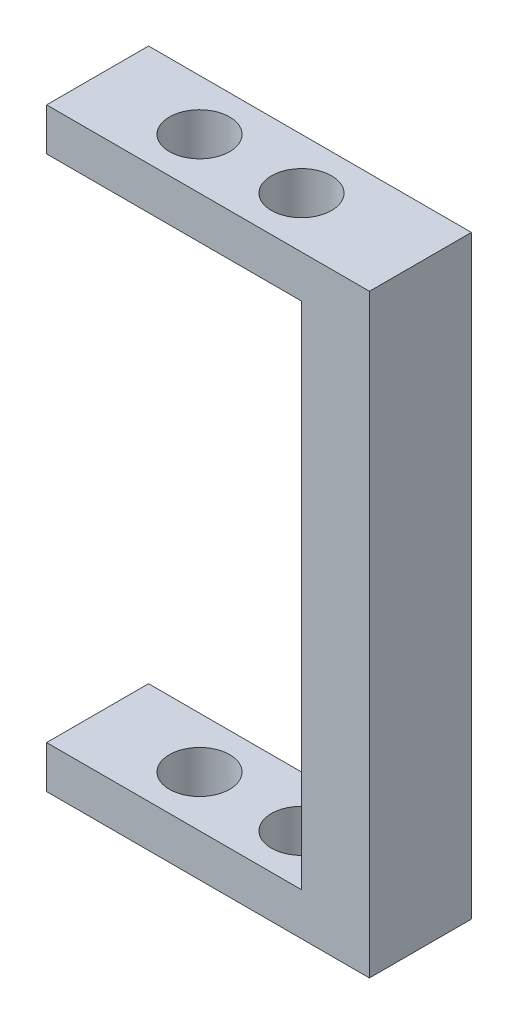
SolidWorks part; units mm, degrees
ref_plane "Front Plane" through (0, 0, 0) normal (0, 0, 1) x (1, 0, 0)
ref_plane "Top Plane" through (0, 0, 0) normal (0, 1, 0) x (1, 0, 0)
ref_plane "Right Plane" through (0, 0, 0) normal (1, 0, 0) x (0, 0, -1)
sketch "Sketch1" plane through (0, 0, 0) normal (0, 0, 1) x (1, 0, 0)
  line L1 (-2.54, -22.225) -> (2.54, -22.225)
  line L2 (-2.54, -22.225) -> (-2.54, 22.225)
  line L3 (-2.54, 22.225) -> (2.54, 22.225)
  line L4 (2.54, -22.225) -> (2.54, 22.225)
  line L5 (-2.54, -22.225) -> (2.54, 22.225) construction
  line L6 (-2.54, 22.225) -> (2.54, -22.225) construction
  line L7 (-2.54, 22.225) -> (-21.59, 22.225)
  line L8 (-2.54, 22.225) -> (-2.54, 19.05)
  line L9 (-2.54, 19.05) -> (-21.59, 19.05)
  line L10 (-21.59, 22.225) -> (-21.59, 19.05)
  line L11 (-2.54, -22.225) -> (-21.59, -22.225)
  line L12 (-2.54, -22.225) -> (-2.54, -19.05)
  line L13 (-2.54, -19.05) -> (-21.59, -19.05)
  line L14 (-21.59, -22.225) -> (-21.59, -19.05)
  point P0 (0, 0)
  dimension "D1" = 44.45
  dimension "D2" = 5.08
  dimension "D3" = 3.175
  dimension "D4" = 3.175
  dimension "D5" = 19.05
  dimension "D6" = 19.05
extrude "Boss-Extrude1" add sketch "Sketch1" along normal blind 7.62 contours L7 L10 L9 L2 | L1 L4 L3 L2 | L14 L11 L2 L13
hole_wizard "M4 Clearance Hole1" positions "Sketch2" profile "Sketch3" hole size "M4" standard "ANSI Metric" end condition through all
sketch "Sketch2" plane through (0, 22.225, 0) normal (0, 1, 0) x (1, 0, 0)
  line L0 (-21.59, -7.62) -> (-21.59, 0) construction
  line L1 (2.54, -7.62) -> (2.54, 0) construction
  point P0 (-13.97, -3.81)
  point P2 (-6.35, -3.81)
  point P8 (-21.59, -3.81)
  point P9 (-8.6451, -3.81)
  point P10 (-15.6519, -3.81)
  dimension "D1" = 8.89
  dimension "D2" = 7.62
sketch "Sketch3" plane through (-13.97, 22.225, 3.81) normal (1, 0, 0) x (0, 0, 1)
  line L0 (0, 0) -> (0, 44.45)
  line L1 (0, 44.45) -> (2.25, 44.45)
  line L2 (2.25, 44.45) -> (2.25, 0)
  line L5 (2.25, 0) -> (0, 0)
  line L11 (0, -6.35) -> (0, 107.95) construction
  dimension "Thru Hole Dia." = 4.5
  dimension "Thru Hole Depth" = 44.45
